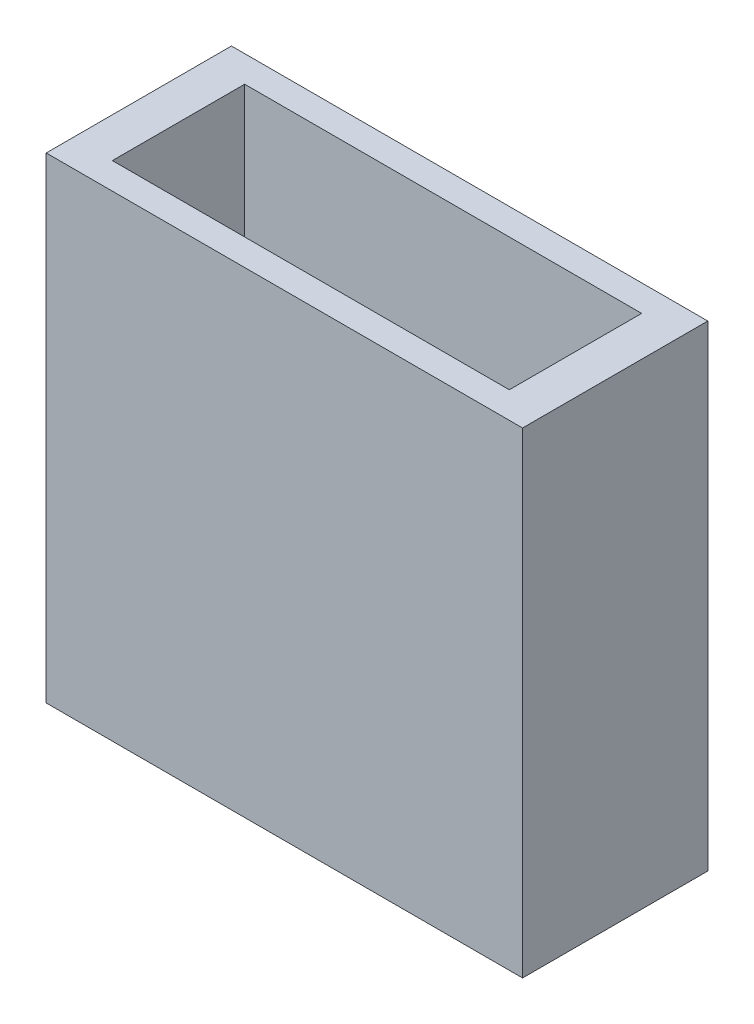
SolidWorks part; units mm, degrees
ref_plane "Front Plane" through (0, 0, 0) normal (0, 0, 1) x (1, 0, 0)
ref_plane "Top Plane" through (0, 0, 0) normal (0, 1, 0) x (1, 0, 0)
ref_plane "Right Plane" through (0, 0, 0) normal (1, 0, 0) x (0, 0, -1)
sketch "Sketch1" plane through (0, 0, 0) normal (0, 1, 0) x (1, 0, 0)
  line L1 (0, 0) -> (45.72, 0)
  line L2 (0, 0) -> (0, 17.78)
  line L3 (0, 17.78) -> (45.72, 17.78)
  line L4 (45.72, 0) -> (45.72, 17.78)
  dimension "D1" = 45.72
  dimension "D2" = 17.78
extrude "Boss-Extrude1" add sketch "Sketch1" along normal blind 45.72
ref_plane "Plane1" through (0, 45.72, 0) normal (0, 1, 0) x (1, 0, 0)
sketch "Sketch2" plane through (0, 45.72, 0) normal (0, 1, 0) x (1, 0, 0)
  line L0 (0, 17.78) -> (0, 0) construction
  line L1 (3.81, 2.54) -> (41.91, 2.54)
  line L2 (3.81, 2.54) -> (3.81, 15.24)
  line L3 (3.81, 15.24) -> (41.91, 15.24)
  line L4 (41.91, 2.54) -> (41.91, 15.24)
  line L5 (45.72, 0) -> (45.72, 17.78) construction
  line L6 (0, 0) -> (45.72, 0) construction
  line L7 (45.72, 17.78) -> (0, 17.78) construction
  dimension "D1" = 3.81
  dimension "D2" = 3.81
  dimension "D3" = 2.54
  dimension "D4" = 2.54
extrude "Cut-Extrude1" cut sketch "Sketch2" against normal blind 41.91
sketch "Sketch4" plane through (0, 0, 0) normal (0, 0, 1) x (1, 0, 0)
  line L0 (0, 0) -> (25.4, -4.7076)
  line L1 (0, 0) -> (45.72, 0) construction
  dimension "D1" = 10.5
  dimension "D2" = 25.4
sketch "Sketch5" plane through (0, 0, 0) normal (0, 1, 0) x (1, 0, 0)
  line L0 (0, 0) -> (3.9734, 25.0873)
  line L1 (0, 0) -> (25.4, 0) construction
  dimension "D1" = 81
  dimension "D2" = 25.4
ref_plane "Plane3" through (0, 0, 0) normal (-0.1822, -0.9828, -0.0289) x (-0.9833, 0.1821, 0.0053)
sketch "Sketch6" plane through (0, 0, 0) normal (-0.1822, -0.9828, -0.0289) x (-0.9833, 0.1821, 0.0053)
  line L0 (-44.9551, 0) -> (-45.0501, 17.7723) construction
  line L1 (-45.0501, 17.7723) -> (-0.095, 17.7723) construction
  circle A0 centre (-22.1422, 8.8823) radius 3.048
  circle A1 centre (-15.0302, 8.8823) radius 3.048
  circle A2 centre (-29.2542, 8.8823) radius 3.048
  dimension "D2" = 6.096
  dimension "D4" = 6.096
  dimension "D5" = 6.096
  dimension "D1" = 22.86
  dimension "D3" = 8.89
  dimension "D6" = 7.112
  dimension "D7" = 7.112
  dimension "D8" = 8.89
  dimension "D9" = 8.89
extrude "Cut-Extrude2" cut sketch "Sketch6" against normal blind 15.24 and the other way through all
equation "\"x\"=0.296138"
